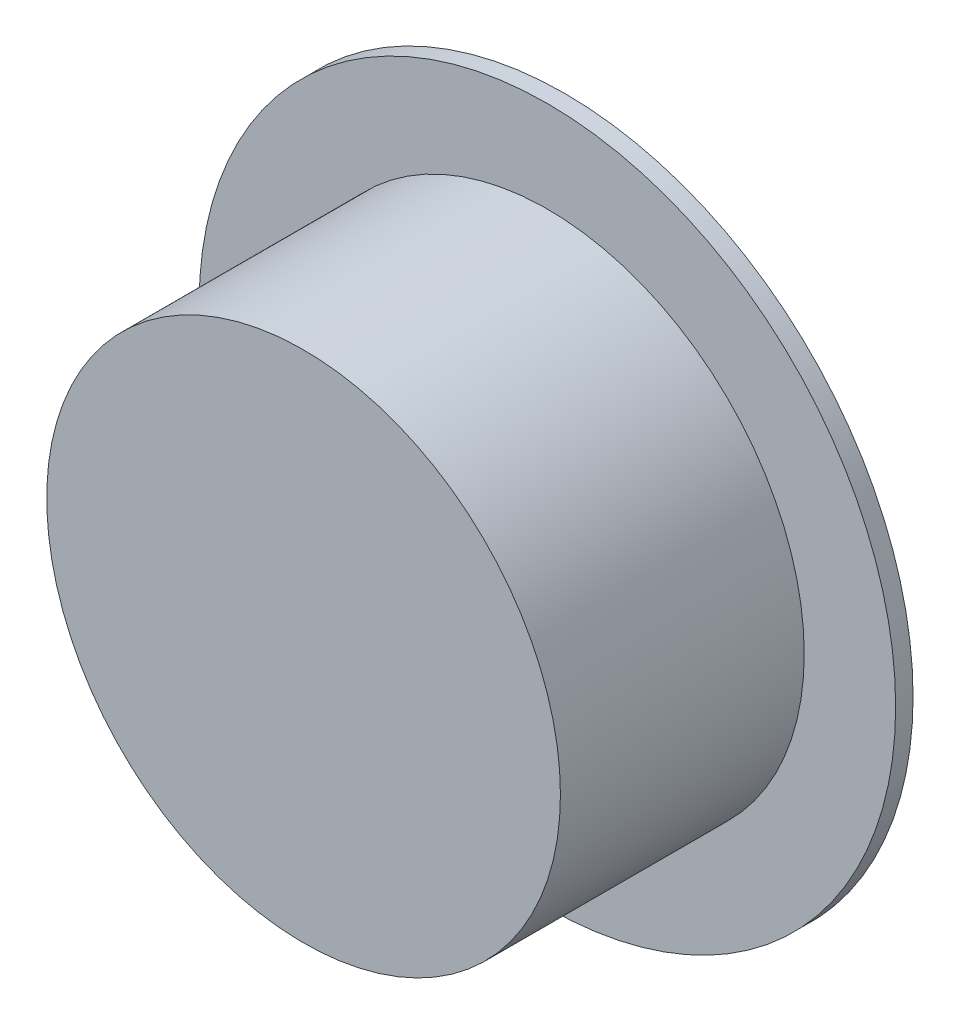
SolidWorks part; units mm, degrees
ref_plane "Front Plane" through (0, 0, 0) normal (0, 0, 1) x (1, 0, 0)
ref_plane "Top Plane" through (0, 0, 0) normal (0, 1, 0) x (1, 0, 0)
ref_plane "Right Plane" through (0, 0, 0) normal (1, 0, 0) x (0, 0, -1)
sketch "Sketch2" plane through (0, 0, 0) normal (0, 0, 1) x (1, 0, 0)
  circle A0 centre (0, 0) radius 14.75
  dimension "D1" = 29.5
extrude "Boss-Extrude1" add sketch "Sketch2" along normal mid plane 15
sketch "Sketch3" plane through (0, 0, 0) normal (0, 0, 1) x (1, 0, 0)
  circle A0 centre (0, 0) radius 20
  dimension "D1" = 40
extrude "Boss-Extrude2" add sketch "Sketch3" along normal blind 1 from surface at -7.5 starting at face at (14.75, 0, -7.5)
sketch "Sketch4" plane through (0, 0, -7.5) normal (0, 0, -1) x (-1, 0, 0)
  circle A0 centre (0, 0) radius 12.5
  dimension "D1" = 25
extrude "Cut-Extrude1" cut sketch "Sketch4" against normal blind 10
